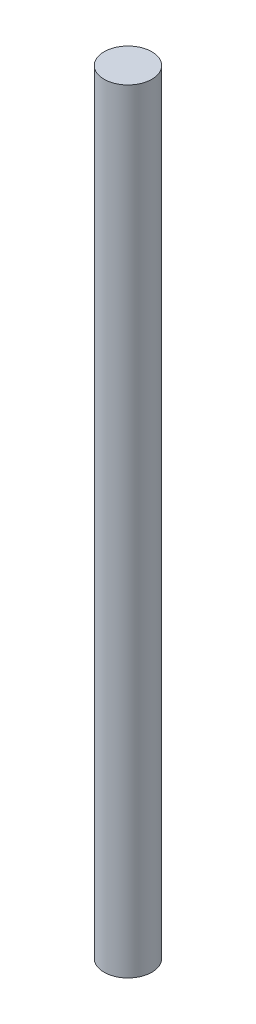
SolidWorks part; units mm, degrees
ref_plane "Front Plane" through (0, 0, 0) normal (0, 0, 1) x (1, 0, 0)
ref_plane "Top Plane" through (0, 0, 0) normal (0, 1, 0) x (1, 0, 0)
ref_plane "Right Plane" through (0, 0, 0) normal (1, 0, 0) x (0, 0, -1)
sketch "Sketch2" plane through (0, 0, 0) normal (0, 1, 0) x (1, 0, 0)
  circle A0 centre (0, 0) radius 5.5562
  dimension "D1" = 11.1125
extrude "Boss-Extrude1" add sketch "Sketch2" along normal blind 180
